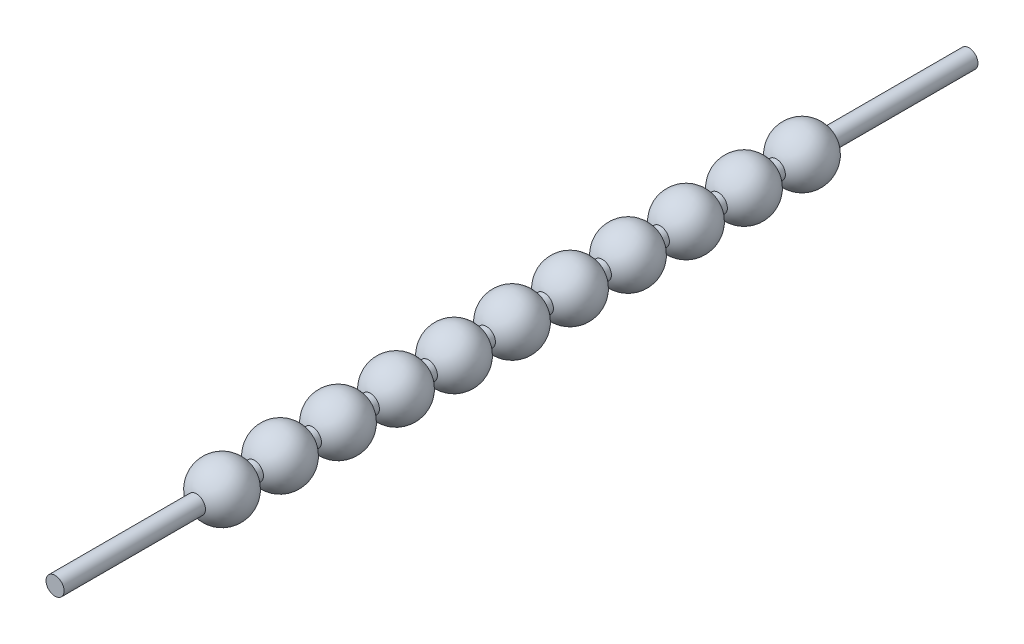
SolidWorks part; units mm, degrees
ref_plane "前视基准面" through (0, 0, 0) normal (0, 0, 1) x (1, 0, 0)
ref_plane "上视基准面" through (0, 0, 0) normal (0, 1, 0) x (1, 0, 0)
ref_plane "右视基准面" through (0, 0, 0) normal (1, 0, 0) x (0, 0, -1)
sketch "草图1" plane through (0, 0, 0) normal (1, 0, 0) x (0, 0, -1)
  line L0 (-0.6525, 0) -> (50.9689, 0) construction
  line L1 (-0.5714, 0) -> (-0.5714, 0.5)
  line L2 (-0.5714, 0.5) -> (7.2286, 0.5)
  line L3 (10.3428, 0.5) -> (10.3428, 0)
  line L4 (10.3428, 0.5) -> (10.4286, 0.5)
  line L5 (49.857, 0.5) -> (49.857, 0)
  line L6 (38.857, 0.5) -> (39.2286, 0.5)
  line L7 (35.657, 0.5) -> (36.0286, 0.5)
  line L8 (32.457, 0.5) -> (32.8286, 0.5)
  line L9 (29.257, 0.5) -> (29.6286, 0.5)
  line L10 (26.057, 0.5) -> (26.4286, 0.5)
  line L11 (22.857, 0.5) -> (23.2286, 0.5)
  line L12 (19.657, 0.5) -> (20.0286, 0.5)
  line L13 (16.457, 0.5) -> (16.8286, 0.5)
  line L14 (13.257, 0.5) -> (13.6286, 0.5)
  line L15 (-0.5714, 0) -> (10.3428, 0)
  line L16 (42.057, 0.5) -> (49.857, 0.5)
  line L17 (13.3428, 0) -> (13.5428, 0)
  line L18 (35.7428, 0) -> (35.9428, 0)
  line L19 (32.5428, 0) -> (32.7428, 0)
  line L20 (29.3428, 0) -> (29.5428, 0)
  line L21 (26.1428, 0) -> (26.3428, 0)
  line L22 (22.9428, 0) -> (23.1428, 0)
  line L23 (16.5428, 0) -> (16.7428, 0)
  line L24 (19.7428, 0) -> (19.9428, 0)
  line L25 (10.057, 0.5) -> (10.3428, 0.5)
  circle A1 centre (11.8428, 0) radius 1.5
  circle A2 centre (15.0428, 0) radius 1.5
  circle A3 centre (18.2428, 0) radius 1.5
  circle A4 centre (21.4428, 0) radius 1.5
  circle A5 centre (24.6428, 0) radius 1.5
  circle A6 centre (27.8428, 0) radius 1.5
  circle A7 centre (31.0428, 0) radius 1.5
  circle A8 centre (34.2428, 0) radius 1.5
  circle A9 centre (37.4428, 0) radius 1.5
  circle A10 centre (40.6428, 0) radius 1.5
  circle A11 centre (8.6428, 0) radius 1.5
  point P70 (50.9689, 0)
  dimension "D1" = 7.8
  dimension "D3" = 3
  dimension "D2" = 0.5
  dimension "D5" = 7.8
  dimension "D4" = 9
  dimension "D6" = 2
  dimension "D7" = 2
revolve "旋转1" add sketch "草图1" angle 360 about L0
